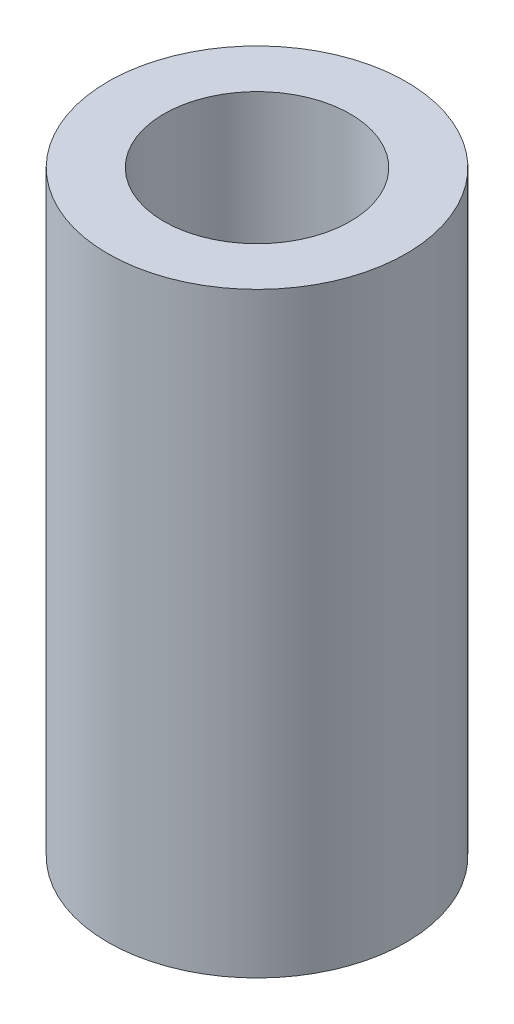
SolidWorks part; units mm, degrees
ref_plane "Front Plane" through (0, 0, 0) normal (0, 0, 1) x (1, 0, 0)
ref_plane "Top Plane" through (0, 0, 0) normal (0, 1, 0) x (1, 0, 0)
ref_plane "Right Plane" through (0, 0, 0) normal (1, 0, 0) x (0, 0, -1)
sketch "Sketch1" plane through (0, 0, 0) normal (0, 1, 0) x (1, 0, 0)
  circle A0 centre (0, 0) radius 8
  circle A1 centre (0, 0) radius 5
  dimension "D1" = 16
  dimension "D2" = 10
extrude "Boss-Extrude1" add sketch "Sketch1" along normal blind 32
